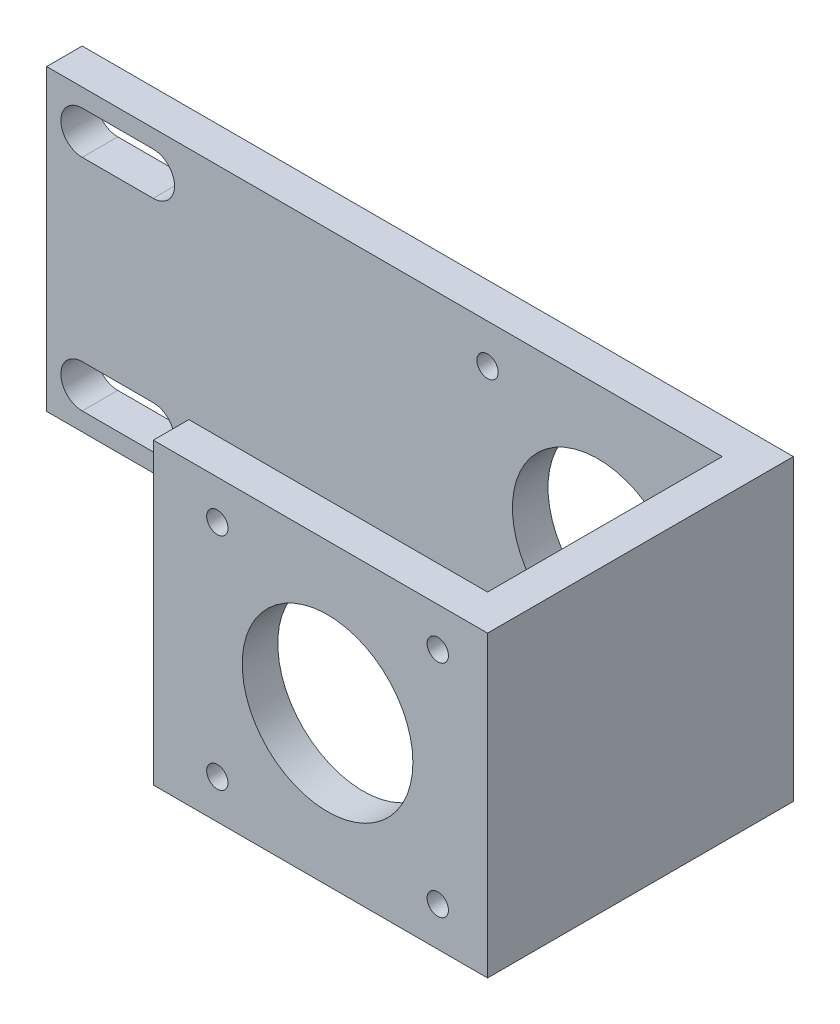
SolidWorks part; units mm, degrees
ref_plane "Alzado" through (0, 0, 0) normal (0, 0, 1) x (1, 0, 0)
ref_plane "Planta" through (0, 0, 0) normal (0, 1, 0) x (1, 0, 0)
ref_plane "Vista lateral" through (0, 0, 0) normal (1, 0, 0) x (0, 0, -1)
sketch "Croquis1" plane through (0, 0, 0) normal (0, 0, 1) x (1, 0, 0)
  line L0 (-45, -21) -> (-45, 21)
  line L1 (-50, 21) -> (50, 21)
  line L2 (-50, 21) -> (-50, -21)
  line L3 (-50, -21) -> (50, -21)
  line L4 (50, 21) -> (50, -21)
  line L5 (-50, 21) -> (50, -21) construction
  line L6 (-50, -21) -> (50, 21) construction
  line L7 (-50, 0) -> (50, 0) construction
  line L8 (-45, 15.44) -> (-35.0214, 15.44) construction
  line L9 (-45, 18.44) -> (-35.0214, 18.44)
  line L10 (-45, 12.44) -> (-35.0214, 12.44)
  line L11 (-45, -15.44) -> (-35.0214, -15.44) construction
  line L12 (-45, -12.44) -> (-35.0214, -12.44)
  line L13 (-45, -18.44) -> (-35.0214, -18.44)
  arc A2 (-45, 18.44) -> (-45, 12.44) centre (-45, 15.44) ccw
  arc A3 (-35.0214, 12.44) -> (-35.0214, 18.44) centre (-35.0214, 15.44) ccw
  arc A4 (-45, -12.44) -> (-45, -18.44) centre (-45, -15.44) ccw
  arc A5 (-35.0214, -18.44) -> (-35.0214, -12.44) centre (-35.0214, -15.44) ccw
  point P0 (0, 0)
  point P14 (-40.0107, 15.44)
  point P20 (-40.0107, -15.44)
  dimension "D4" = 15.44
  dimension "D5" = 3
  dimension "D6" = 3
  dimension "D1" = 42
  dimension "D2" = 100
  dimension "D3" = 5
extrude "Saliente-Extruir1" add sketch "Croquis1" along normal blind 5
sketch "Croquis2" plane through (0, 0, 5) normal (0, 0, 1) x (1, 0, 0)
  line L0 (-50, -21) -> (50, -21) construction
  line L1 (50, 21) -> (45, 21)
  line L2 (50, 21) -> (50, -21)
  line L3 (50, -21) -> (45, -21)
  line L4 (45, 21) -> (45, -21)
  dimension "D1" = 5
extrude "Saliente-Extruir2" add sketch "Croquis2" along normal blind 38
sketch "Croquis3" plane through (45, 0, 0) normal (-1, 0, 0) x (0, 0, 1)
  line L0 (43, 21) -> (5, 21) construction
  line L1 (43, -21) -> (38, -21)
  line L2 (43, -21) -> (43, 21)
  line L3 (43, 21) -> (38, 21)
  line L4 (38, -21) -> (38, 21)
  dimension "D1" = 5
sketch "Croquis4" plane through (0, 0, 5) normal (0, 0, 1) x (1, 0, 0)
  line L0 (22.5, -21) -> (22.5, 21) construction
  line L4 (-50, -21) -> (45, -21) construction
  line L5 (-50, 21) -> (45, 21) construction
  line L6 (-50, 21) -> (-50, -21) construction
  dimension "D1" = 72.5
extrude "Saliente-Extruir3" add sketch "Croquis3" along normal blind 42
sketch "Croquis7" plane through (0, 0, 43) normal (0, 0, 1) x (1, 0, 0)
  line L0 (22.5, -21) -> (22.5, 21) construction
  line L3 (3, -21) -> (3, 21) construction
  line L5 (12, 15.5) -> (43, 15.5)
  line L6 (12, 15.5) -> (12, -15.5)
  line L7 (12, -15.5) -> (43, -15.5)
  line L8 (43, 15.5) -> (43, -15.5)
  line L9 (12, 15.5) -> (43, -15.5) construction
  line L10 (12, -15.5) -> (43, 15.5) construction
  circle A0 centre (12, 15.5) radius 1.5
  circle A1 centre (43, 15.5) radius 1.5
  circle A2 centre (43, -15.5) radius 1.5
  circle A3 centre (12, -15.5) radius 1.5
  circle A4 centre (27.5, 0) radius 12
  point P8 (22.5, 0)
  dimension "D4" = 3
  dimension "D6" = 24
  dimension "D1" = 19.5
  dimension "D2" = 31
  dimension "D3" = 31
  dimension "D5" = 9
extrude "Cortar-Extruir1" cut sketch "Croquis7" against normal up to surface (43 mm away) contours L6 A3 L7 | L7 A3 L6 | A0 | A1 | A2 up to face at (-40.0107, -15.44, 0)
sketch "Croquis8" plane through (0, 0, 43) normal (0, 0, 1) x (1, 0, 0)
  line L0 (12, 15.5) -> (43, -15.5) construction
  circle A0 centre (27.5, 0) radius 12
  dimension "D1" = 24
extrude "Cortar-Extruir2" cut sketch "Croquis8" against normal up to surface (43 mm away) up to face at (44.5, -15.5, 0)
sketch "Croquis11" plane through (0, 0, 43) normal (0, 0, 1) x (1, 0, 0)
  line L0 (27.5, 0) -> (-50, 0)
  line L1 (-50, 21) -> (-50, -21) construction
